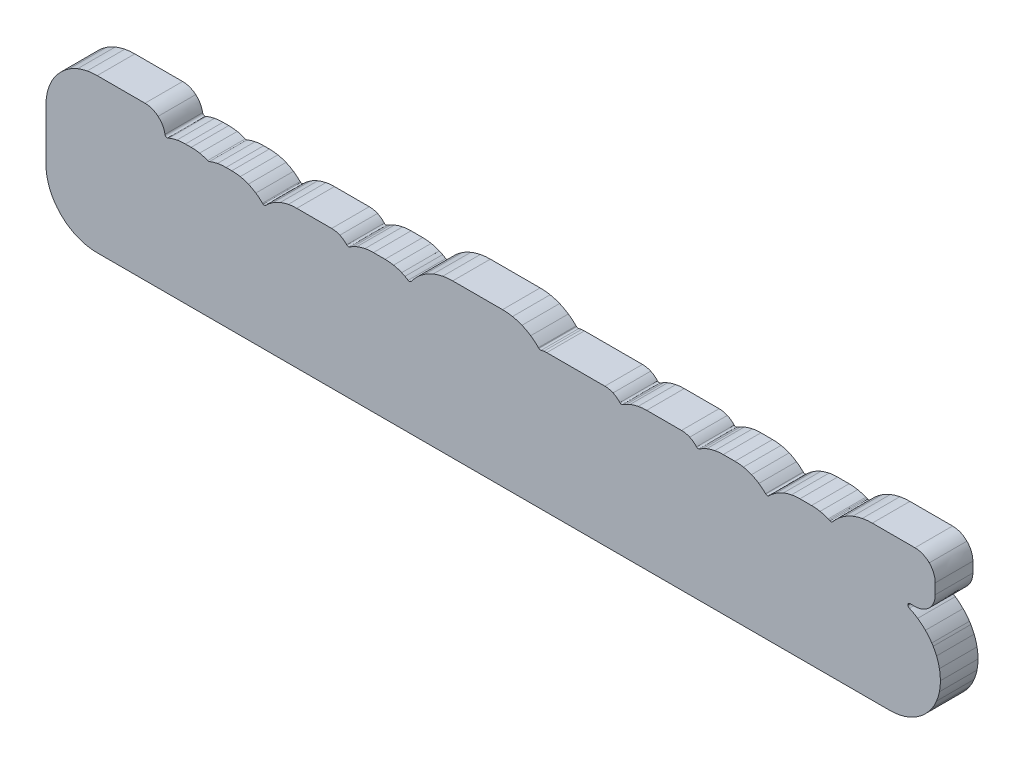
SolidWorks part; units mm, degrees
ref_plane "Plano frontal" through (0, 0, 0) normal (0, 0, 1) x (1, 0, 0)
ref_plane "Plano superior" through (0, 0, 0) normal (0, 1, 0) x (1, 0, 0)
ref_plane "Plano direito" through (0, 0, 0) normal (1, 0, 0) x (0, 0, -1)
sketch "Esboço1" plane through (0, 0, 0) normal (0, 0, 1) x (1, 0, 0)
  line L1 (-356.4626, 0.4183) -> (-356.4626, 20.5242)
  line L2 (-315.6765, 61.1642) -> (-277.5585, 61.1642)
  line L3 (-259.0592, 46.3085) -> (-258.606, 46.4993)
  line L4 (-258.606, 46.4993) -> (-258.6058, 46.4988)
  line L5 (-245.3538, 49.1139) -> (-240.774, 49.1139)
  line L6 (-212.9831, 49.1139) -> (-208.4029, 49.1139)
  line L7 (-181.2229, 38.8574) -> (-181.216, 38.8643)
  line L8 (-181.216, 38.8643) -> (-181.1091, 38.9712)
  line L9 (-181.1091, 38.9712) -> (-181.1058, 38.9679)
  line L10 (-175.8503, 43.2895) -> (-175.784, 43.3357)
  line L11 (-156.5669, 49.1139) -> (-128.7752, 49.1139)
  line L12 (-95.4677, 49.1139) -> (-86.2035, 49.1139)
  line L13 (-72.9524, 46.5013) -> (-72.9534, 46.4988)
  line L14 (-65.3598, 44.2511) -> (-65.3588, 44.2504)
  line L15 (-32.2697, 61.1642) -> (7.4407, 61.1642)
  line L16 (36.1668, 49.199) -> (36.42, 48.9435)
  line L17 (42.6822, 49.1139) -> (89.0011, 49.1139)
  line L18 (122.3094, 49.1139) -> (150.1005, 49.1139)
  line L19 (183.4091, 49.1139) -> (192.6725, 49.1139)
  line L20 (205.9241, 46.5013) -> (205.9229, 46.4988)
  line L21 (217.0953, 38.9679) -> (217.2678, 38.7965)
  line L22 (219.7992, 38.8033) -> (219.9665, 38.9712)
  line L23 (219.9665, 38.9712) -> (219.9698, 38.9679)
  line L24 (225.2243, 43.2913) -> (225.2254, 43.2897)
  line L25 (244.5088, 49.1139) -> (253.7722, 49.1139)
  line L26 (267.7681, 46.1851) -> (267.7704, 46.1838)
  line L27 (267.7704, 46.1838) -> (267.7681, 46.1782)
  line L28 (302.1881, 61.165) -> (336.2013, 61.165)
  line L29 (352.3577, 45.0083) -> (352.3577, 36.7988)
  line L30 (336.2013, 20.6423) -> (332.3293, 20.6423)
  line L39 (-356.4626, 0.4183) -> (-356.4626, -20.525)
  line L40 (-315.6765, -61.165) -> (-289.8043, -61.165)
  line L41 (-289.8043, -61.165) -> (-277.5585, -61.165)
  line L42 (-277.5585, -61.165) -> (-49.877, -61.165)
  line L43 (-49.877, -61.165) -> (-30.3814, -61.165)
  line L44 (-30.3814, -61.165) -> (5.5522, -61.165)
  line L45 (5.5522, -61.165) -> (28.9349, -61.165)
  line L46 (28.9349, -61.165) -> (281.6631, -61.165)
  line L47 (281.6631, -61.165) -> (315.8221, -61.165)
  spline S0 degree 3 poles (-356.4626, 20.5242) (-356.4626, 23.2654) (-356.2076, 25.9316) (-355.698, 28.5217) knots 0.015385 0.015385 0.015385 0.015385 0.023077 0.023077 0.023077 0.023077
  spline S1 degree 3 poles (-355.698, 28.5217) (-355.1875, 31.1163) (-354.4225, 33.6408) (-353.4047, 36.0926) knots 0.023077 0.023077 0.023077 0.023077 0.030769 0.030769 0.030769 0.030769
  spline S2 degree 3 poles (-353.4047, 36.0926) (-352.3839, 38.5511) (-351.137, 40.8742) (-349.6661, 43.0599) knots 0.030769 0.030769 0.030769 0.030769 0.038462 0.038462 0.038462 0.038462
  spline S3 degree 3 poles (-349.6661, 43.0599) (-348.2025, 45.2349) (-346.4954, 47.2978) (-344.5454, 49.2476) knots 0.038462 0.038462 0.038462 0.038462 0.046154 0.046154 0.046154 0.046154
  spline S4 degree 3 poles (-344.5454, 49.2476) (-342.6082, 51.1848) (-340.5408, 52.8876) (-338.346, 54.353) knots 0.046154 0.046154 0.046154 0.046154 0.053846 0.053846 0.053846 0.053846
  spline S5 degree 3 poles (-338.346, 54.353) (-336.1383, 55.8272) (-333.786, 57.0786) (-331.2909, 58.1063) knots 0.053846 0.053846 0.053846 0.053846 0.061538 0.061538 0.061538 0.061538
  spline S6 degree 3 poles (-331.2909, 58.1063) (-328.8226, 59.1223) (-326.282, 59.8871) (-323.6699, 60.3999) knots 0.061538 0.061538 0.061538 0.061538 0.069231 0.069231 0.069231 0.069231
  spline S7 degree 3 poles (-323.6699, 60.3999) (-321.074, 60.9092) (-318.4088, 61.1642) (-315.6765, 61.1642) knots 0.069231 0.069231 0.069231 0.069231 0.076923 0.076923 0.076923 0.076923
  spline S8 degree 3 poles (-277.5585, 61.1642) (-273.5699, 61.1642) (-269.92, 59.7215) (-267.1041, 57.3316) knots 0.084615 0.084615 0.084615 0.084615 0.092308 0.092308 0.092308 0.092308
  spline S9 degree 3 poles (-267.1041, 57.3316) (-264.2436, 54.9031) (-262.2387, 51.4965) (-261.6088, 47.6316) knots 0.092308 0.092308 0.092308 0.092308 0.1 0.1 0.1 0.1
  spline S10 degree 3 poles (-261.6088, 47.6316) (-261.4501, 46.6557) (-260.5298, 45.9933) (-259.554, 46.1518) knots 0.1 0.1 0.1 0.1 0.107692 0.107692 0.107692 0.107692
  spline S11 degree 3 poles (-259.554, 46.1518) (-259.3777, 46.1808) (-259.2118, 46.2346) (-259.0592, 46.3085) knots 0.107692 0.107692 0.107692 0.107692 0.115385 0.115385 0.115385 0.115385
  spline S12 degree 3 poles (-258.6058, 46.4988) (-256.5004, 47.368) (-254.3378, 48.0217) (-252.1212, 48.4602) knots 0.130769 0.130769 0.130769 0.130769 0.138462 0.138462 0.138462 0.138462
  spline S13 degree 3 poles (-252.1212, 48.4602) (-249.918, 48.8958) (-247.6617, 49.1139) (-245.3538, 49.1139) knots 0.138462 0.138462 0.138462 0.138462 0.146154 0.146154 0.146154 0.146154
  spline S14 degree 3 poles (-240.774, 49.1139) (-238.4628, 49.1139) (-236.2111, 48.8993) (-234.0199, 48.4706) knots 0.153846 0.153846 0.153846 0.153846 0.161538 0.161538 0.161538 0.161538
  spline S15 degree 3 poles (-234.0199, 48.4706) (-231.8111, 48.0388) (-229.6648, 47.3946) (-227.5845, 46.5404) knots 0.161538 0.161538 0.161538 0.161538 0.169231 0.169231 0.169231 0.169231
  spline S16 degree 3 poles (-227.5845, 46.5404) (-227.1306, 46.354) (-226.6447, 46.3677) (-226.2238, 46.5404) knots 0.169231 0.169231 0.169231 0.169231 0.176923 0.176923 0.176923 0.176923
  spline S17 degree 3 poles (-226.2238, 46.5404) (-224.1507, 47.3964) (-222.0095, 48.0405) (-219.8017, 48.4706) knots 0.176923 0.176923 0.176923 0.176923 0.184615 0.184615 0.184615 0.184615
  spline S18 degree 3 poles (-219.8017, 48.4706) (-217.6023, 48.8993) (-215.3285, 49.1139) (-212.9831, 49.1139) knots 0.184615 0.184615 0.184615 0.184615 0.192308 0.192308 0.192308 0.192308
  spline S19 degree 3 poles (-208.4029, 49.1139) (-206.0948, 49.1139) (-203.8388, 48.8958) (-201.6354, 48.4602) knots 0.2 0.2 0.2 0.2 0.207692 0.207692 0.207692 0.207692
  spline S20 degree 3 poles (-201.6354, 48.4602) (-199.4187, 48.0217) (-197.2567, 47.3677) (-195.1512, 46.4988) knots 0.207692 0.207692 0.207692 0.207692 0.215385 0.215385 0.215385 0.215385
  spline S21 degree 3 poles (-195.1512, 46.4988) (-193.0634, 45.6369) (-191.0806, 44.5757) (-189.2049, 43.3164) knots 0.215385 0.215385 0.215385 0.215385 0.223077 0.223077 0.223077 0.223077
  spline S22 degree 3 poles (-189.2049, 43.3164) (-187.3311, 42.0578) (-185.5605, 40.5966) (-183.893, 38.9329) knots 0.223077 0.223077 0.223077 0.223077 0.230769 0.230769 0.230769 0.230769
  spline S23 degree 3 poles (-183.893, 38.9329) (-183.74, 38.781) (-183.5666, 38.6621) (-183.3817, 38.5768) knots 0.230769 0.230769 0.230769 0.230769 0.238462 0.238462 0.238462 0.238462
  spline S24 degree 3 poles (-183.3817, 38.5768) (-182.6986, 38.181) (-181.8091, 38.2742) (-181.2229, 38.8574) knots 0.238462 0.238462 0.238462 0.238462 0.246154 0.246154 0.246154 0.246154
  spline S25 degree 3 poles (-181.1058, 38.9679) (-179.4698, 40.6042) (-177.7172, 42.0449) (-175.8503, 43.2895) knots 0.269231 0.269231 0.269231 0.269231 0.276923 0.276923 0.276923 0.276923
  spline S26 degree 3 poles (-175.784, 43.3357) (-173.9217, 44.5722) (-171.9321, 45.6268) (-169.8186, 46.4988) knots 0.284615 0.284615 0.284615 0.284615 0.292308 0.292308 0.292308 0.292308
  spline S27 degree 3 poles (-169.8186, 46.4988) (-167.7129, 47.3677) (-165.5508, 48.0217) (-163.3339, 48.4602) knots 0.292308 0.292308 0.292308 0.292308 0.3 0.3 0.3 0.3
  spline S28 degree 3 poles (-163.3339, 48.4602) (-161.1307, 48.8958) (-158.875, 49.1139) (-156.5669, 49.1139) knots 0.3 0.3 0.3 0.3 0.307692 0.307692 0.307692 0.307692
  spline S29 degree 3 poles (-128.7752, 49.1139) (-126.4298, 49.1139) (-124.2106, 48.6209) (-122.2162, 47.7337) knots 0.315385 0.315385 0.315385 0.315385 0.323077 0.323077 0.323077 0.323077
  spline S30 degree 3 poles (-122.2162, 47.7337) (-120.1367, 46.8094) (-118.2855, 45.4533) (-116.7752, 43.7797) knots 0.323077 0.323077 0.323077 0.323077 0.330769 0.330769 0.330769 0.330769
  spline S31 degree 3 poles (-116.7752, 43.7797) (-116.1527, 43.0883) (-115.1138, 42.9946) (-114.3803, 43.5356) knots 0.330769 0.330769 0.330769 0.330769 0.338462 0.338462 0.338462 0.338462
  spline S32 degree 3 poles (-114.3803, 43.5356) (-113.5146, 44.0964) (-112.6127, 44.6232) (-111.6774, 45.1142) knots 0.338462 0.338462 0.338462 0.338462 0.346154 0.346154 0.346154 0.346154
  spline S33 degree 3 poles (-111.6774, 45.1142) (-110.7087, 45.623) (-109.7216, 46.0853) (-108.7194, 46.4988) knots 0.346154 0.346154 0.346154 0.346154 0.353846 0.353846 0.353846 0.353846
  spline S34 degree 3 poles (-108.7194, 46.4988) (-106.614, 47.3677) (-104.4519, 48.0217) (-102.2347, 48.4602) knots 0.353846 0.353846 0.353846 0.353846 0.361538 0.361538 0.361538 0.361538
  spline S35 degree 3 poles (-102.2347, 48.4602) (-100.0313, 48.8958) (-97.7753, 49.1139) (-95.4677, 49.1139) knots 0.361538 0.361538 0.361538 0.361538 0.369231 0.369231 0.369231 0.369231
  spline S36 degree 3 poles (-86.2035, 49.1139) (-83.8853, 49.1139) (-81.6234, 48.8958) (-79.4189, 48.4602) knots 0.376923 0.376923 0.376923 0.376923 0.384615 0.384615 0.384615 0.384615
  spline S37 degree 3 poles (-79.4189, 48.4602) (-77.2048, 48.0225) (-75.0484, 47.3687) (-72.9524, 46.5013) knots 0.384615 0.384615 0.384615 0.384615 0.392308 0.392308 0.392308 0.392308
  spline S38 degree 3 poles (-72.9534, 46.4988) (-72.0278, 46.1152) (-71.1449, 45.7043) (-70.3095, 45.2674) knots 0.4 0.4 0.4 0.4 0.407692 0.407692 0.407692 0.407692
  spline S39 degree 3 poles (-70.3095, 45.2674) (-69.4708, 44.8292) (-68.6265, 44.3377) (-67.7779, 43.7949) knots 0.407692 0.407692 0.407692 0.407692 0.415385 0.415385 0.415385 0.415385
  spline S40 degree 3 poles (-67.7779, 43.7949) (-66.9742, 43.2791) (-65.9127, 43.4866) (-65.3598, 44.2511) knots 0.415385 0.415385 0.415385 0.415385 0.423077 0.423077 0.423077 0.423077
  spline S41 degree 3 poles (-65.3588, 44.2504) (-64.0852, 46.0075) (-62.6491, 47.6857) (-61.0519, 49.2831) knots 0.430769 0.430769 0.430769 0.430769 0.438462 0.438462 0.438462 0.438462
  spline S42 degree 3 poles (-61.0519, 49.2831) (-59.1198, 51.215) (-57.0591, 52.9123) (-54.8703, 54.3735) knots 0.438462 0.438462 0.438462 0.438462 0.446154 0.446154 0.446154 0.446154
  spline S43 degree 3 poles (-54.8703, 54.3735) (-52.6699, 55.8429) (-50.3235, 57.0906) (-47.8358, 58.1149) knots 0.446154 0.446154 0.446154 0.446154 0.453846 0.453846 0.453846 0.453846
  spline S44 degree 3 poles (-47.8358, 58.1149) (-45.3758, 59.1282) (-42.8424, 59.8907) (-40.2387, 60.402) knots 0.453846 0.453846 0.453846 0.453846 0.461538 0.461538 0.461538 0.461538
  spline S45 degree 3 poles (-40.2387, 60.402) (-37.6507, 60.91) (-34.9936, 61.1642) (-32.2697, 61.1642) knots 0.461538 0.461538 0.461538 0.461538 0.469231 0.469231 0.469231 0.469231
  spline S46 degree 3 poles (7.4407, 61.1642) (10.1732, 61.1642) (12.8316, 60.91) (15.4132, 60.402) knots 0.476923 0.476923 0.476923 0.476923 0.484615 0.484615 0.484615 0.484615
  spline S47 degree 3 poles (15.4132, 60.402) (18.0002, 59.8929) (20.5171, 59.1302) (22.9616, 58.1149) knots 0.484615 0.484615 0.484615 0.484615 0.492308 0.492308 0.492308 0.492308
  spline S48 degree 3 poles (22.9616, 58.1149) (25.4124, 57.0974) (27.7289, 55.8543) (29.9077, 54.3883) knots 0.492308 0.492308 0.492308 0.492308 0.5 0.5 0.5 0.5
  spline S49 degree 3 poles (29.9077, 54.3883) (32.0764, 52.9288) (34.1333, 51.227) (36.0771, 49.2831) knots 0.5 0.5 0.5 0.5 0.507692 0.507692 0.507692 0.507692
  spline S50 degree 3 poles (36.0771, 49.2831) (36.1061, 49.2539) (36.1363, 49.226) (36.1668, 49.199) knots 0.507692 0.507692 0.507692 0.507692 0.515385 0.515385 0.515385 0.515385
  spline S51 degree 3 poles (36.42, 48.9435) (36.9148, 48.4457) (37.6298, 48.3001) (38.2539, 48.5069) knots 0.523077 0.523077 0.523077 0.523077 0.530769 0.530769 0.530769 0.530769
  spline S52 degree 3 poles (38.2539, 48.5069) (38.9425, 48.7025) (39.6598, 48.8544) (40.401, 48.9588) knots 0.530769 0.530769 0.530769 0.530769 0.538462 0.538462 0.538462 0.538462
  spline S53 degree 3 poles (40.401, 48.9588) (41.1272, 49.0609) (41.8889, 49.1139) (42.6822, 49.1139) knots 0.538462 0.538462 0.538462 0.538462 0.546154 0.546154 0.546154 0.546154
  spline S54 degree 3 poles (89.0011, 49.1139) (91.3468, 49.1139) (93.5662, 48.6207) (95.5604, 47.7337) knots 0.553846 0.553846 0.553846 0.553846 0.561538 0.561538 0.561538 0.561538
  spline S55 degree 3 poles (95.5604, 47.7337) (97.6399, 46.8089) (99.491, 45.4528) (101.0011, 43.7794) knots 0.561538 0.561538 0.561538 0.561538 0.569231 0.569231 0.569231 0.569231
  spline S56 degree 3 poles (101.0011, 43.7794) (101.6236, 43.0881) (102.6627, 42.9943) (103.3963, 43.5353) knots 0.569231 0.569231 0.569231 0.569231 0.576923 0.576923 0.576923 0.576923
  spline S57 degree 3 poles (103.3963, 43.5353) (104.2619, 44.0962) (105.1639, 44.6227) (106.0991, 45.114) knots 0.576923 0.576923 0.576923 0.576923 0.584615 0.584615 0.584615 0.584615
  spline S58 degree 3 poles (106.0991, 45.114) (107.0681, 45.6227) (108.0552, 46.0853) (109.0579, 46.4988) knots 0.584615 0.584615 0.584615 0.584615 0.592308 0.592308 0.592308 0.592308
  spline S59 degree 3 poles (109.0579, 46.4988) (111.1634, 47.3677) (113.3254, 48.0217) (115.5423, 48.4602) knots 0.592308 0.592308 0.592308 0.592308 0.6 0.6 0.6 0.6
  spline S60 degree 3 poles (115.5423, 48.4602) (117.7455, 48.8958) (120.0015, 49.1139) (122.3094, 49.1139) knots 0.6 0.6 0.6 0.6 0.607692 0.607692 0.607692 0.607692
  spline S61 degree 3 poles (150.1005, 49.1139) (152.4465, 49.1139) (154.6659, 48.6207) (156.6601, 47.7337) knots 0.615385 0.615385 0.615385 0.615385 0.623077 0.623077 0.623077 0.623077
  spline S62 degree 3 poles (156.6601, 47.7337) (158.7391, 46.8089) (160.5907, 45.4528) (162.1008, 43.7792) knots 0.623077 0.623077 0.623077 0.623077 0.630769 0.630769 0.630769 0.630769
  spline S63 degree 3 poles (162.1008, 43.7792) (162.7233, 43.0875) (163.7624, 42.9938) (164.496, 43.5348) knots 0.630769 0.630769 0.630769 0.630769 0.638462 0.638462 0.638462 0.638462
  spline S64 degree 3 poles (164.496, 43.5348) (165.3611, 44.0954) (166.2638, 44.6225) (167.1988, 45.1137) knots 0.638462 0.638462 0.638462 0.638462 0.646154 0.646154 0.646154 0.646154
  spline S65 degree 3 poles (167.1988, 45.1137) (168.1681, 45.6227) (169.1546, 46.0847) (170.1574, 46.4988) knots 0.646154 0.646154 0.646154 0.646154 0.653846 0.653846 0.653846 0.653846
  spline S66 degree 3 poles (170.1574, 46.4988) (172.2633, 47.3677) (174.4254, 48.0217) (176.642, 48.4602) knots 0.653846 0.653846 0.653846 0.653846 0.661538 0.661538 0.661538 0.661538
  spline S67 degree 3 poles (176.642, 48.4602) (178.8455, 48.8958) (181.1012, 49.1139) (183.4091, 49.1139) knots 0.661538 0.661538 0.661538 0.661538 0.669231 0.669231 0.669231 0.669231
  spline S68 degree 3 poles (192.6725, 49.1139) (194.9907, 49.1139) (197.2531, 48.8958) (199.4576, 48.4602) knots 0.676923 0.676923 0.676923 0.676923 0.684615 0.684615 0.684615 0.684615
  spline S69 degree 3 poles (199.4576, 48.4602) (201.6717, 48.0225) (203.8281, 47.3687) (205.9241, 46.5013) knots 0.684615 0.684615 0.684615 0.684615 0.692308 0.692308 0.692308 0.692308
  spline S70 degree 3 poles (205.9229, 46.4988) (207.9605, 45.6542) (209.9114, 44.6042) (211.7735, 43.3494) knots 0.7 0.7 0.7 0.7 0.707692 0.707692 0.707692 0.707692
  spline S71 degree 3 poles (211.7735, 43.3494) (213.648, 42.0863) (215.4227, 40.6253) (217.0953, 38.9679) knots 0.707692 0.707692 0.707692 0.707692 0.715385 0.715385 0.715385 0.715385
  spline S72 degree 3 poles (217.2678, 38.7965) (217.9686, 38.0995) (219.1024, 38.1023) (219.7992, 38.8033) knots 0.723077 0.723077 0.723077 0.723077 0.730769 0.730769 0.730769 0.730769
  spline S73 degree 3 poles (219.9698, 38.9679) (221.6084, 40.6067) (223.3602, 42.0479) (225.2243, 43.2913) knots 0.746154 0.746154 0.746154 0.746154 0.753846 0.753846 0.753846 0.753846
  spline S74 degree 3 poles (225.2254, 43.2897) (227.1156, 44.5496) (229.1265, 45.6194) (231.2571, 46.4988) knots 0.761538 0.761538 0.761538 0.761538 0.769231 0.769231 0.769231 0.769231
  spline S75 degree 3 poles (231.2571, 46.4988) (233.3625, 47.3677) (235.5245, 48.0217) (237.7412, 48.4602) knots 0.769231 0.769231 0.769231 0.769231 0.776923 0.776923 0.776923 0.776923
  spline S76 degree 3 poles (237.7412, 48.4602) (239.9447, 48.8958) (242.2007, 49.1139) (244.5088, 49.1139) knots 0.776923 0.776923 0.776923 0.776923 0.784615 0.784615 0.784615 0.784615
  spline S77 degree 3 poles (253.7722, 49.1139) (256.0904, 49.1139) (258.3525, 48.8958) (260.557, 48.4602) knots 0.792308 0.792308 0.792308 0.792308 0.8 0.8 0.8 0.8
  spline S78 degree 3 poles (260.557, 48.4602) (262.7734, 48.022) (264.9317, 47.3677) (267.0294, 46.4988) knots 0.8 0.8 0.8 0.8 0.807692 0.807692 0.807692 0.807692
  spline S79 degree 3 poles (267.0294, 46.4988) (267.3388, 46.3705) (267.588, 46.2646) (267.7681, 46.1851) knots 0.807692 0.807692 0.807692 0.807692 0.815385 0.815385 0.815385 0.815385
  spline S80 degree 3 poles (267.7681, 46.1782) (268.0472, 46.0543) (268.2918, 45.9425) (268.4993, 45.8447) knots 0.830769 0.830769 0.830769 0.830769 0.838462 0.838462 0.838462 0.838462
  spline S81 degree 3 poles (268.4993, 45.8447) (269.2893, 45.4718) (270.2149, 45.7271) (270.7107, 46.4083) knots 0.838462 0.838462 0.838462 0.838462 0.846154 0.846154 0.846154 0.846154
  spline S82 degree 3 poles (270.7107, 46.4083) (271.0739, 46.8432) (271.4833, 47.3098) (271.9388, 47.8089) knots 0.846154 0.846154 0.846154 0.846154 0.853846 0.853846 0.853846 0.853846
  spline S83 degree 3 poles (271.9388, 47.8089) (272.3533, 48.263) (272.8135, 48.7434) (273.318, 49.2478) knots 0.853846 0.853846 0.853846 0.853846 0.861538 0.861538 0.861538 0.861538
  spline S84 degree 3 poles (273.318, 49.2478) (275.2552, 51.1856) (277.3225, 52.8884) (279.5173, 54.354) knots 0.861538 0.861538 0.861538 0.861538 0.869231 0.869231 0.869231 0.869231
  spline S85 degree 3 poles (279.5173, 54.354) (281.7251, 55.8279) (284.0774, 57.0794) (286.573, 58.1071) knots 0.869231 0.869231 0.869231 0.869231 0.876923 0.876923 0.876923 0.876923
  spline S86 degree 3 poles (286.573, 58.1071) (289.0411, 59.1228) (291.5823, 59.8879) (294.1942, 60.4004) knots 0.876923 0.876923 0.876923 0.876923 0.884615 0.884615 0.884615 0.884615
  spline S87 degree 3 poles (294.1942, 60.4004) (296.7904, 60.91) (299.4558, 61.165) (302.1881, 61.165) knots 0.884615 0.884615 0.884615 0.884615 0.892308 0.892308 0.892308 0.892308
  spline S88 degree 3 poles (336.2013, 61.165) (340.6625, 61.165) (344.7024, 59.356) (347.6257, 56.433) knots 0.9 0.9 0.9 0.9 0.907692 0.907692 0.907692 0.907692
  spline S89 degree 3 poles (347.6257, 56.433) (350.549, 53.5097) (352.3577, 49.4698) (352.3577, 45.0083) knots 0.907692 0.907692 0.907692 0.907692 0.915385 0.915385 0.915385 0.915385
  spline S90 degree 3 poles (352.3577, 36.7988) (352.3577, 32.3375) (350.549, 28.2976) (347.6257, 25.3743) knots 0.923077 0.923077 0.923077 0.923077 0.930769 0.930769 0.930769 0.930769
  spline S91 degree 3 poles (347.6257, 25.3743) (344.7024, 22.4511) (340.6625, 20.6423) (336.2013, 20.6423) knots 0.930769 0.930769 0.930769 0.930769 0.938462 0.938462 0.938462 0.938462
  spline S92 degree 3 poles (332.3293, 20.6423) (331.3382, 20.6423) (330.5343, 19.8384) (330.5343, 18.8471) knots 0.946154 0.946154 0.946154 0.946154 0.953846 0.953846 0.953846 0.953846
  spline S93 degree 3 poles (330.5343, 18.8471) (330.5343, 18.0485) (331.0562, 17.3718) (331.7771, 17.1389) knots 0.953846 0.953846 0.953846 0.953846 0.961538 0.961538 0.961538 0.961538
  spline S94 degree 3 poles (331.7771, 17.1389) (334.0593, 16.1633) (336.2582, 14.9509) (338.3722, 13.5037) knots 0.961538 0.961538 0.961538 0.961538 0.969231 0.969231 0.969231 0.969231
  spline S95 degree 3 poles (338.3722, 13.5037) (340.5154, 12.0363) (342.5736, 10.316) (344.5454, 8.3442) knots 0.969231 0.969231 0.969231 0.969231 0.976923 0.976923 0.976923 0.976923
  spline S96 degree 3 poles (344.5454, 8.3442) (346.4834, 6.4061) (348.186, 4.3388) (349.6516, 2.144) knots 0.976923 0.976923 0.976923 0.976923 0.984615 0.984615 0.984615 0.984615
  spline S97 degree 3 poles (349.6516, 2.144) (350.0295, 1.5784) (350.3922, 1.003) (350.741, 0.4183) knots 0.984615 0.984615 0.984615 0.984615 1 1 1 1
  spline S117 degree 3 poles (-356.4626, -20.525) (-356.4626, -23.2661) (-356.2076, -25.9324) (-355.698, -28.5219) knots 0.033333 0.033333 0.033333 0.033333 0.066667 0.066667 0.066667 0.066667
  spline S118 degree 3 poles (-355.698, -28.5219) (-355.1875, -31.1165) (-354.4227, -33.6408) (-353.4047, -36.0929) knots 0.066667 0.066667 0.066667 0.066667 0.1 0.1 0.1 0.1
  spline S119 degree 3 poles (-353.4047, -36.0929) (-352.3839, -38.5514) (-351.1372, -40.8747) (-349.6661, -43.0606) knots 0.1 0.1 0.1 0.1 0.133333 0.133333 0.133333 0.133333
  spline S120 degree 3 poles (-349.6661, -43.0606) (-348.2022, -45.2359) (-346.4946, -47.2991) (-344.5454, -49.2481) knots 0.133333 0.133333 0.133333 0.133333 0.166667 0.166667 0.166667 0.166667
  spline S121 degree 3 poles (-344.5454, -49.2481) (-342.6074, -51.1861) (-340.5401, -52.8886) (-338.3453, -54.3542) knots 0.166667 0.166667 0.166667 0.166667 0.2 0.2 0.2 0.2
  spline S122 degree 3 poles (-338.3453, -54.3542) (-336.138, -55.8284) (-333.7855, -57.0796) (-331.2907, -58.1071) knots 0.2 0.2 0.2 0.2 0.233333 0.233333 0.233333 0.233333
  spline S123 degree 3 poles (-331.2907, -58.1071) (-328.8223, -59.1231) (-326.2815, -59.8879) (-323.6692, -60.4007) knots 0.233333 0.233333 0.233333 0.233333 0.266667 0.266667 0.266667 0.266667
  spline S124 degree 3 poles (-323.6692, -60.4007) (-321.0733, -60.9097) (-318.4086, -61.165) (-315.6765, -61.165) knots 0.266667 0.266667 0.266667 0.266667 0.3 0.3 0.3 0.3
  spline S125 degree 3 poles (315.8221, -61.165) (318.5632, -61.165) (321.2295, -60.91) (323.8195, -60.4007) knots 0.566667 0.566667 0.566667 0.566667 0.6 0.6 0.6 0.6
  spline S126 degree 3 poles (323.8195, -60.4007) (326.4139, -59.8902) (328.9384, -59.1254) (331.3905, -58.1071) knots 0.6 0.6 0.6 0.6 0.633333 0.633333 0.633333 0.633333
  spline S127 degree 3 poles (331.3905, -58.1071) (333.8487, -57.0865) (336.172, -55.8399) (338.3582, -54.3684) knots 0.633333 0.633333 0.633333 0.633333 0.666667 0.666667 0.666667 0.666667
  spline S128 degree 3 poles (338.3582, -54.3684) (340.5332, -52.9046) (342.5967, -51.1973) (344.5454, -49.2481) knots 0.666667 0.666667 0.666667 0.666667 0.7 0.7 0.7 0.7
  spline S129 degree 3 poles (344.5454, -49.2481) (346.4946, -47.2984) (348.2025, -45.2351) (349.6663, -43.0596) knots 0.7 0.7 0.7 0.7 0.733333 0.733333 0.733333 0.733333
  spline S130 degree 3 poles (349.6663, -43.0596) (351.1372, -40.8739) (352.3839, -38.5508) (353.4047, -36.0929) knots 0.733333 0.733333 0.733333 0.733333 0.766667 0.766667 0.766667 0.766667
  spline S131 degree 3 poles (353.4047, -36.0929) (354.423, -33.6405) (355.1875, -31.1153) (355.698, -28.5206) knots 0.766667 0.766667 0.766667 0.766667 0.8 0.8 0.8 0.8
  spline S132 degree 3 poles (355.698, -28.5206) (356.2073, -25.9314) (356.4626, -23.2654) (356.4626, -20.525) knots 0.8 0.8 0.8 0.8 0.833333 0.833333 0.833333 0.833333
  spline S133 degree 3 poles (356.4626, -20.525) (356.4626, -17.793) (356.2073, -15.1282) (355.698, -12.5324) knots 0.833333 0.833333 0.833333 0.833333 0.866667 0.866667 0.866667 0.866667
  spline S134 degree 3 poles (355.698, -12.5324) (355.1855, -9.9197) (354.4204, -7.3784) (353.4047, -4.9106) knots 0.866667 0.866667 0.866667 0.866667 0.9 0.9 0.9 0.9
  spline S135 degree 3 poles (353.4047, -4.9106) (352.6376, -3.0528) (351.7522, -1.2776) (350.741, 0.4183) knots 0.9 0.9 0.9 0.9 0.933333 0.933333 0.933333 0.933333
  dimension "D1" = 227.6815
extrude "Ressalto-extrusão2" add sketch "Esboço1" along normal blind 30
